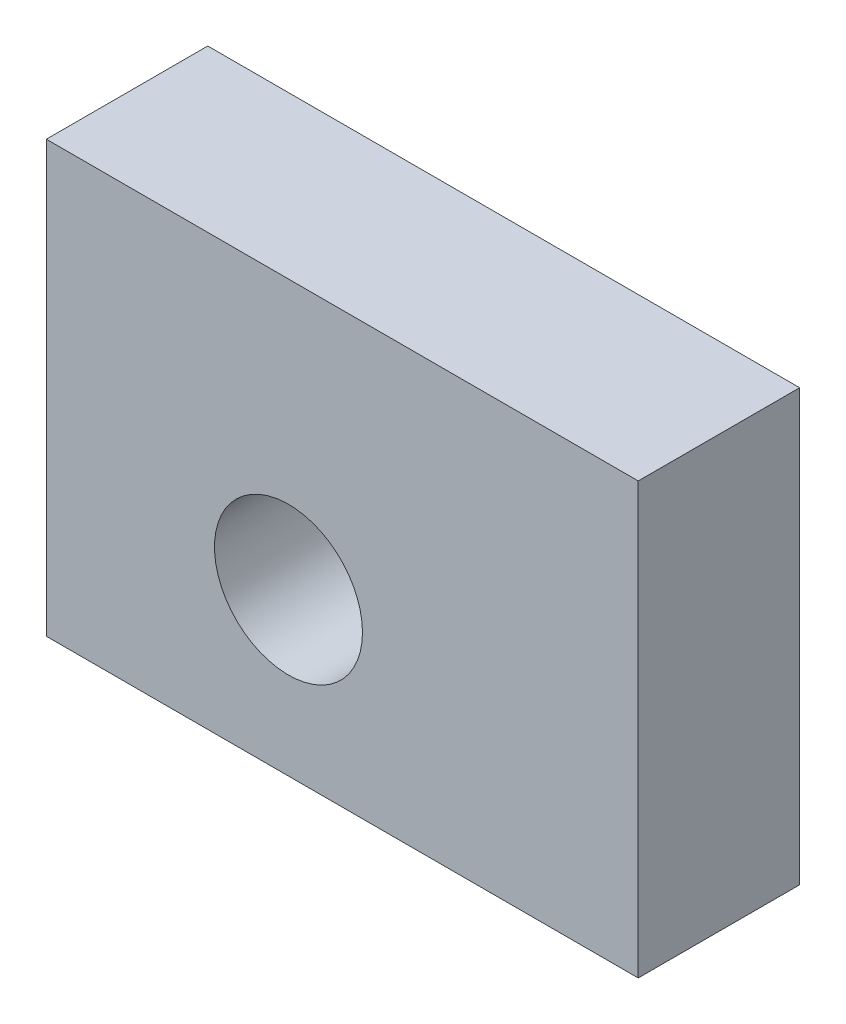
SolidWorks part; units mm, degrees
material "ABS PC"
ref_plane "Front Plane" through (0, 0, 0) normal (0, 0, 1) x (1, 0, 0)
ref_plane "Top Plane" through (0, 0, 0) normal (0, 1, 0) x (1, 0, 0)
ref_plane "Right Plane" through (0, 0, 0) normal (1, 0, 0) x (0, 0, -1)
sketch "Sketch2" plane through (0, 0, 0) normal (0, 0, 1) x (1, 0, 0)
  line L0 (0, 0) -> (0, 16)
  line L1 (0, 0) -> (22, 0)
  line L2 (0, 16) -> (22, 16)
  line L3 (22, 0) -> (22, 16)
  circle A0 centre (9, 6) radius 2.75
  dimension "D3" = 5.5
  dimension "D4" = 6
  dimension "D5" = 9
  dimension "D1" = 22
  dimension "D2" = 16
extrude "Boss-Extrude1" add sketch "Sketch2" along normal blind 6
